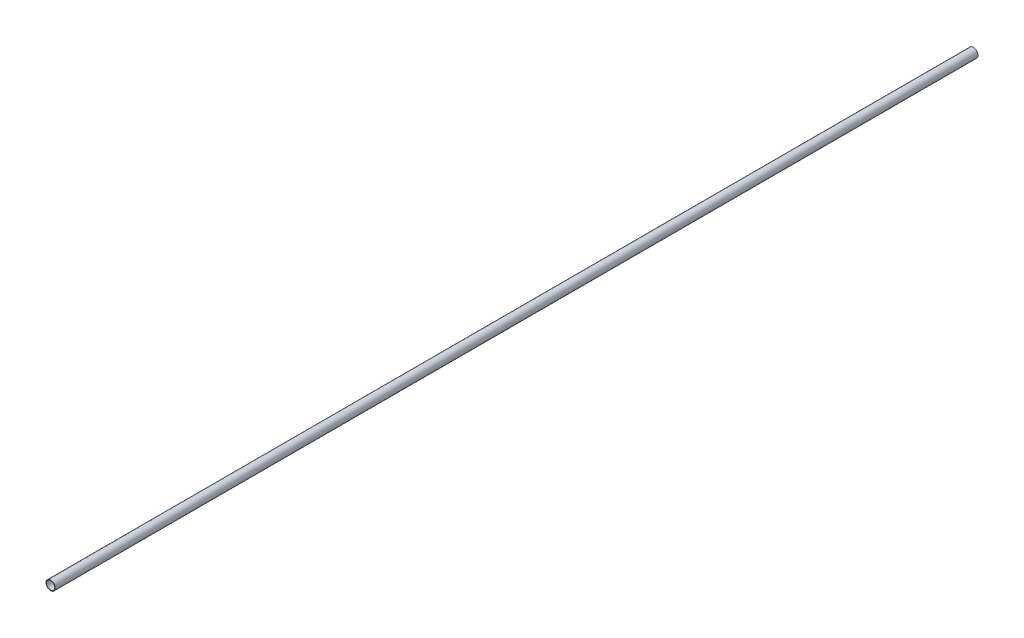
SolidWorks part; units mm, degrees
material "carbon fiber"
ref_plane "Front Plane" through (0, 0, 0) normal (0, 0, 1) x (1, 0, 0)
ref_plane "Top Plane" through (0, 0, 0) normal (0, 1, 0) x (1, 0, 0)
ref_plane "Right Plane" through (0, 0, 0) normal (1, 0, 0) x (0, 0, -1)
sketch "Эскиз1" plane through (0, 0, 0) normal (0, 0, 1) x (1, 0, 0)
  circle A0 centre (0, 0) radius 10
  circle A1 centre (0, 0) radius 9
  dimension "D1" = 20
  dimension "D2" = 1
extrude "Бобышка-Вытянуть1" add sketch "Эскиз1" along normal mid plane 2000
